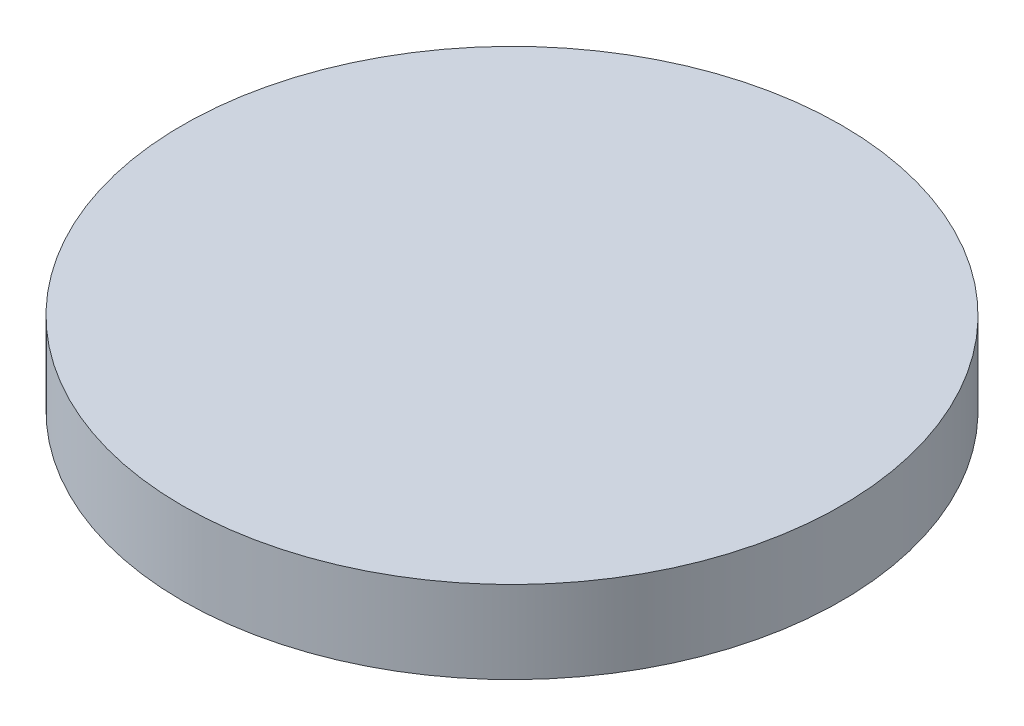
SolidWorks part; units mm, degrees
ref_plane "Front" through (0, 0, 0) normal (0, 0, 1) x (1, 0, 0)
ref_plane "Top" through (0, 0, 0) normal (0, 1, 0) x (1, 0, 0)
ref_plane "Right" through (0, 0, 0) normal (1, 0, 0) x (0, 0, -1)
sketch "X-Y Servo Mount Sketch" plane through (0, 0, 0) normal (0, 1, 0) x (1, 0, 0)
  circle A0 centre (0, 0) radius 12.7
  dimension "D1" = 25.4
extrude "X-Y Servo Mount" add sketch "X-Y Servo Mount Sketch" along normal blind 3.175
